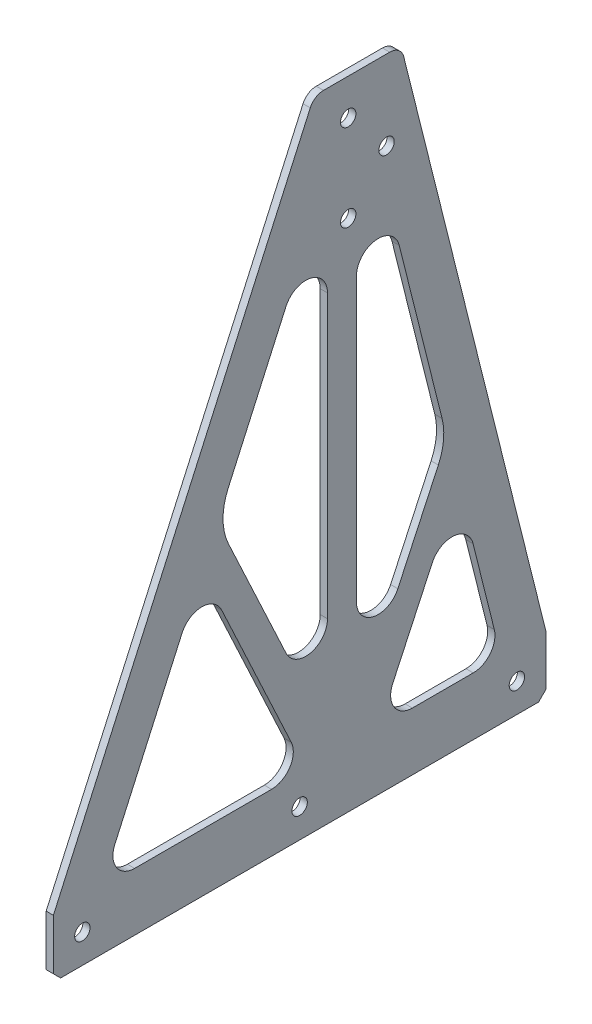
SolidWorks part; units mm, degrees
material "6061-T6 (SS)"
ref_plane "Front Plane" through (0, 0, 0) normal (0, 0, 1) x (1, 0, 0)
ref_plane "Top Plane" through (0, 0, 0) normal (0, 1, 0) x (1, 0, 0)
ref_plane "Right Plane" through (0, 0, 0) normal (1, 0, 0) x (0, 0, -1)
sketch "Sketch1" plane through (0, 0, 0) normal (1, 0, 0) x (0, 0, -1)
  line L1 (118.4058, 279.4) -> (147.4421, 279.4)
  line L2 (153.6025, 274.5901) -> (215.9, 25.4)
  line L3 (215.9, 25.4) -> (215.9, 0)
  line L4 (215.9, 0) -> (0, 0)
  line L5 (0, 25.4) -> (0, 0)
  line L6 (112.6151, 275.6558) -> (0, 25.4)
  arc A0 (112.6151, 275.6558) -> (118.4058, 279.4) centre (118.4058, 273.05) cw
  arc A1 (147.4421, 279.4) -> (153.6025, 274.5901) centre (147.4421, 273.05) cw
  point P2 (114.3, 279.4)
  point P12 (152.4, 279.4)
  dimension "D4" = 6.35
  dimension "D1" = 114.3
  dimension "D2" = 279.4
  dimension "D3" = 215.9
  dimension "D5" = 25.4
  dimension "D6" = 63.5
extrude "Boss-Extrude1" add sketch "Sketch1" along normal blind 3.175
sketch "Sketch2" [suppressed] plane through (3.175, 0, 0) normal (1, 0, 0) x (0, 0, -1)
  line L0 (-279.4, 0) -> (279.4, 0) construction
  line L1 (254, 0) -> (228.6, 0)
  line L2 (254, 0) -> (254, 19.05)
  line L3 (247.65, 25.4) -> (234.95, 25.4)
  line L4 (228.6, 0) -> (228.6, 19.05)
  line L6 (203.2, 0) -> (177.8, 0)
  line L7 (203.2, 0) -> (203.2, 19.05)
  line L8 (196.85, 25.4) -> (184.15, 25.4)
  line L9 (177.8, 0) -> (177.8, 19.05)
  line L10 (152.4, 0) -> (127, 0)
  line L11 (152.4, 0) -> (152.4, 19.05)
  line L12 (146.05, 25.4) -> (133.35, 25.4)
  line L13 (127, 0) -> (127, 19.05)
  line L14 (101.6, 0) -> (76.2, 0)
  line L15 (101.6, 0) -> (101.6, 19.05)
  line L16 (95.25, 25.4) -> (82.55, 25.4)
  line L17 (76.2, 0) -> (76.2, 19.05)
  line L18 (50.8, 0) -> (25.4, 0)
  line L19 (50.8, 0) -> (50.8, 19.05)
  line L20 (44.45, 25.4) -> (31.75, 25.4)
  line L21 (25.4, 0) -> (25.4, 19.05)
  line L22 (50.8, 0) -> (76.2, 0) construction
  line L23 (101.6, 0) -> (127, 0) construction
  line L24 (152.4, 0) -> (177.8, 0) construction
  line L25 (203.2, 0) -> (228.6, 0) construction
  line L27 (279.4, 0) -> (279.4, 12.7) construction
  line L28 (0, 609.6) -> (0, 0) construction
  arc A0 (31.75, 25.4) -> (25.4, 19.05) centre (31.75, 19.05) ccw
  arc A1 (50.8, 19.05) -> (44.45, 25.4) centre (44.45, 19.05) ccw
  arc A2 (82.55, 25.4) -> (76.2, 19.05) centre (82.55, 19.05) ccw
  arc A3 (101.6, 19.05) -> (95.25, 25.4) centre (95.25, 19.05) ccw
  arc A4 (133.35, 25.4) -> (127, 19.05) centre (133.35, 19.05) ccw
  arc A5 (152.4, 19.05) -> (146.05, 25.4) centre (146.05, 19.05) ccw
  arc A6 (184.15, 25.4) -> (177.8, 19.05) centre (184.15, 19.05) ccw
  arc A7 (203.2, 19.05) -> (196.85, 25.4) centre (196.85, 19.05) ccw
  arc A8 (234.95, 25.4) -> (228.6, 19.05) centre (234.95, 19.05) ccw
  arc A9 (254, 19.05) -> (247.65, 25.4) centre (247.65, 19.05) ccw
  point P52 (254, 25.4)
  dimension "D5" = 6.35
  dimension "D1" = 25.4
  dimension "D2" = 25.4
  dimension "D3" = 25.4
  dimension "D4" = 25.4
extrude "Cut-Extrude1" [suppressed] cut sketch "Sketch2" against normal through all
sketch "Sketch3" plane through (3.175, 0, 0) normal (1, 0, 0) x (0, 0, -1)
  line L0 (0, 0) -> (215.9, 0) construction
  line L3 (215.9, 0) -> (215.9, 25.4) construction
  circle A0 centre (146.05, 244.475) radius 3.3782
  circle A1 centre (129.2495, 225.425) radius 3.3782
  circle A2 centre (129.2495, 263.525) radius 3.3782
  dimension "D1" = 6.7564
  dimension "D2" = 244.475
  dimension "D3" = 69.85
  dimension "D4" = 25.4
  dimension "D5" = 25.4
  dimension "D6" = 38.1
extrude "Cut-Extrude2" cut sketch "Sketch3" against normal through all
sketch "Sketch4" plane through (3.175, 0, 0) normal (1, 0, 0) x (0, 0, -1)
  line L0 (0, 0) -> (215.9, 0) construction
  line L1 (0, 25.4) -> (0, 0) construction
  line L2 (215.9, 0) -> (215.9, 25.4) construction
  line L3 (12.7, 12.7) -> (203.2, 12.7) construction
  circle A0 centre (12.7, 12.7) radius 3.3782
  circle A1 centre (107.95, 12.7) radius 3.3782
  circle A2 centre (203.2, 12.7) radius 3.3782
  dimension "D1" = 12.7
  dimension "D2" = 12.7
  dimension "D3" = 12.7
  dimension "D4" = 6.7564
extrude "Cut-Extrude3" cut sketch "Sketch4" against normal through all
chamfer "Chamfer1" distance 3.175 angle 45 2 edges at (1.5875, 0, 0) (1.5875, 0, -215.9)
sketch "Sketch5" plane through (3.175, 0, 0) normal (1, 0, 0) x (0, 0, -1)
  line L0 (35.6212, 25.4) -> (95.6554, 25.4)
  line L1 (101.9521, 205.5382) -> (76.6069, 149.2154)
  line L2 (151.6288, 203.9396) -> (170.3972, 128.8662)
  line L3 (215.9, 25.4) -> (153.6025, 274.5901) construction
  line L4 (112.6151, 275.6558) -> (0, 25.4) construction
  line L5 (120.1632, 77.9211) -> (120.1632, 201.6295)
  line L6 (132.8632, 77.9211) -> (132.8632, 201.6295)
  line L7 (157.371, 25.4) -> (184.0643, 25.4)
  line L8 (3.175, 0) -> (212.725, 0) construction
  line L9 (102.0056, 73.8956) -> (76.7495, 128.0576)
  line L10 (104.2879, 38.9504) -> (73.7366, 104.4679)
  line L11 (151.0208, 73.8956) -> (168.7758, 111.9713)
  line L12 (148.7385, 38.9504) -> (166.1155, 76.2155)
  line L13 (89.3775, 100.9766) -> (77.8674, 95.6094) construction
  line L14 (159.8983, 92.9335) -> (171.4084, 87.5662) construction
  line L15 (110.6066, 25.4) -> (120.1632, 34.9566) construction
  line L16 (115.3849, 30.1783) -> (120.1632, 25.4) construction
  line L17 (183.9886, 74.5002) -> (193.3049, 37.2352)
  line L18 (56.418, 104.3512) -> (26.9351, 38.8337)
  line L19 (132.8632, 34.9566) -> (142.4198, 25.4) construction
  line L20 (137.6415, 30.1783) -> (125.4553, 17.9921) construction
  arc A0 (184.0643, 25.4) -> (193.3049, 37.2352) centre (184.0643, 34.925) ccw
  arc A1 (35.6212, 25.4) -> (26.9351, 38.8337) centre (35.6212, 34.925) cw
  arc A2 (132.8632, 201.6295) -> (151.6288, 203.9396) centre (142.3882, 201.6295) cw
  arc A3 (101.9521, 205.5382) -> (120.1632, 201.6295) centre (110.6382, 201.6295) cw
  arc A4 (166.1155, 76.2155) -> (183.9886, 74.5002) centre (174.748, 72.1901) cw
  arc A5 (73.7366, 104.4679) -> (56.418, 104.3512) centre (65.104, 100.4425) ccw
  arc A6 (104.2879, 38.9504) -> (95.6554, 25.4) centre (95.6554, 34.925) cw
  arc A7 (148.7385, 38.9504) -> (157.371, 25.4) centre (157.371, 34.925) ccw
  arc A8 (151.0208, 73.8956) -> (132.8632, 77.9211) centre (142.3882, 77.9211) cw
  arc A9 (102.0056, 73.8956) -> (120.1632, 77.9211) centre (110.6382, 77.9211) ccw
  arc A10 (168.7758, 111.9713) -> (170.3972, 128.8662) centre (145.7555, 122.7058) ccw
  arc A11 (76.7495, 128.0576) -> (76.6069, 149.2154) centre (99.7697, 138.7921) cw
  point P37 (177.4715, 100.5687)
  point P40 (64.9499, 123.3111)
  dimension "D8" = 9.525
  dimension "D9" = 9.525
  dimension "D10" = 25.4
  dimension "D1" = 25.4
  dimension "D2" = 19.05
  dimension "D3" = 19.05
  dimension "D4" = 12.7
  dimension "D5" = 12.7
  dimension "D6" = 65
  dimension "D7" = 65
extrude "Cut-Extrude4" cut sketch "Sketch5" against normal through all
